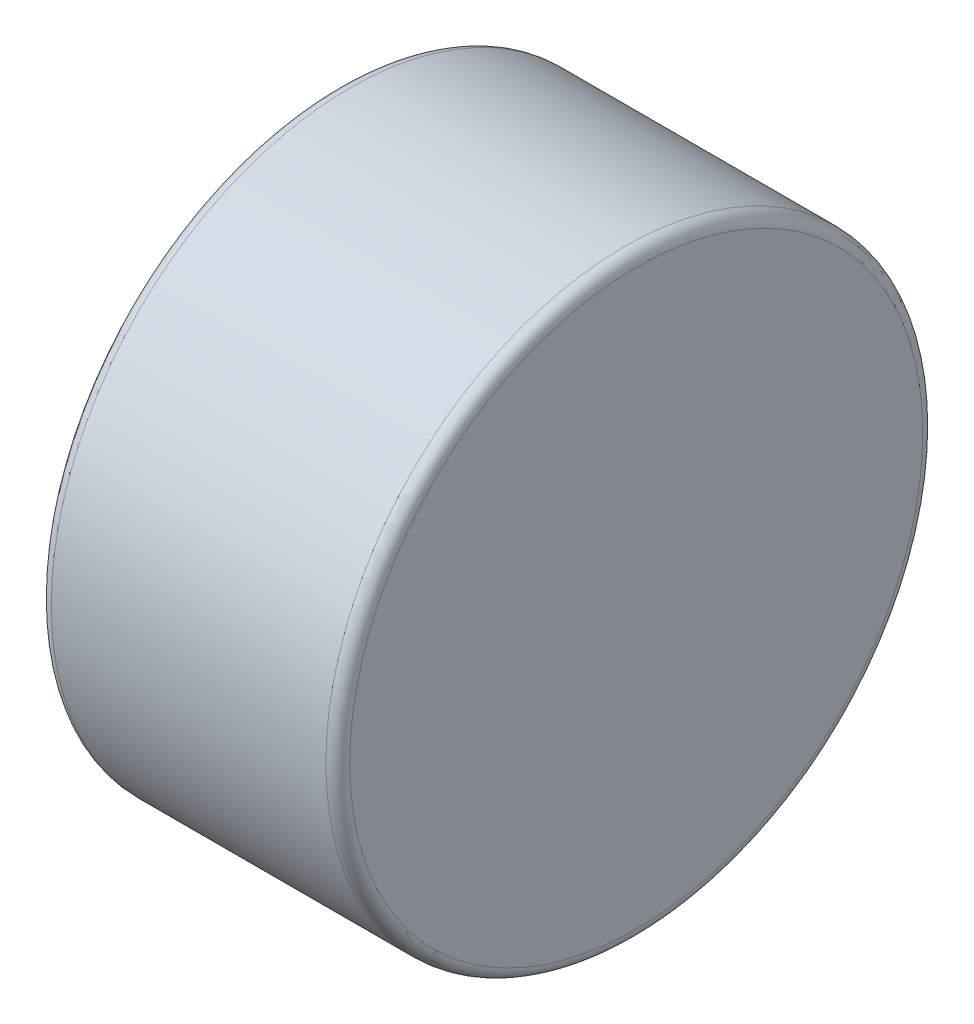
SolidWorks part; units mm, degrees
ref_plane "Front Plane" through (0, 0, 0) normal (0, 0, 1) x (1, 0, 0)
ref_plane "Top Plane" through (0, 0, 0) normal (0, 1, 0) x (1, 0, 0)
ref_plane "Right Plane" through (0, 0, 0) normal (1, 0, 0) x (0, 0, -1)
sketch "Sketch1" plane through (0, 0, 0) normal (1, 0, 0) x (0, 0, -1)
  circle A0 centre (0, 0) radius 5
  dimension "D1" = 10
extrude "Boss-Extrude1" add sketch "Sketch1" along normal mid plane 5
fillet "Fillet1" radius 0.2 2 edges at (2.5, 0, -5) (-2.5, 0, -5)
